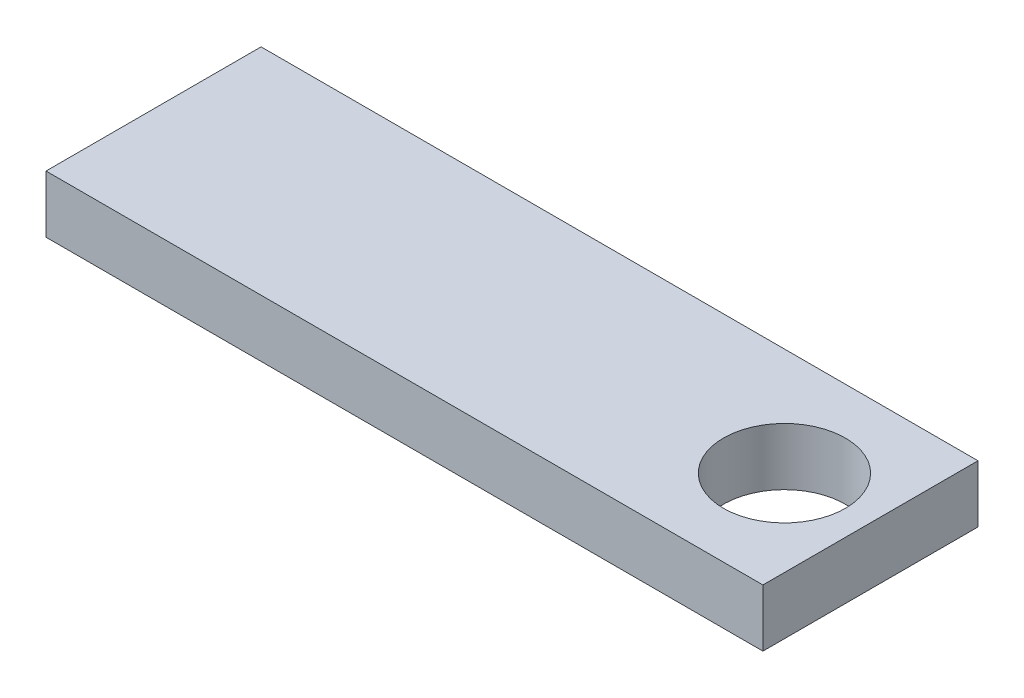
SolidWorks part; units mm, degrees
ref_plane "Front Plane" through (0, 0, 0) normal (0, 0, 1) x (1, 0, 0)
ref_plane "Top Plane" through (0, 0, 0) normal (0, 1, 0) x (1, 0, 0)
ref_plane "Right Plane" through (0, 0, 0) normal (1, 0, 0) x (0, 0, -1)
sketch "Sketch1" plane through (0, 0, 0) normal (0, 1, 0) x (1, 0, 0)
  line L0 (-25, -7.5) -> (-25, 7.5)
  line L1 (-25, -7.5) -> (25, -7.5)
  line L2 (-25, 7.5) -> (25, 7.5)
  line L3 (25, -7.5) -> (25, 7.5)
  line L4 (0, 7.5) -> (0, -7.5) construction
  line L5 (-25, 0) -> (25, 0) construction
  point P1 (0, 0)
  dimension "D1" = 15
  dimension "D2" = 50
extrude "Boss-Extrude1" add sketch "Sketch1" along normal blind 4
sketch "Sketch2" plane through (0, 4, 0) normal (0, 1, 0) x (1, 0, 0)
  line L0 (25, 0) -> (0, 0) construction
  line L1 (25, -7.5) -> (25, 7.5) construction
  circle A0 centre (19, 0) radius 4.25
  dimension "D1" = 8.5
  dimension "D2" = 6
extrude "Cut-Extrude1" cut sketch "Sketch2" against normal through all
